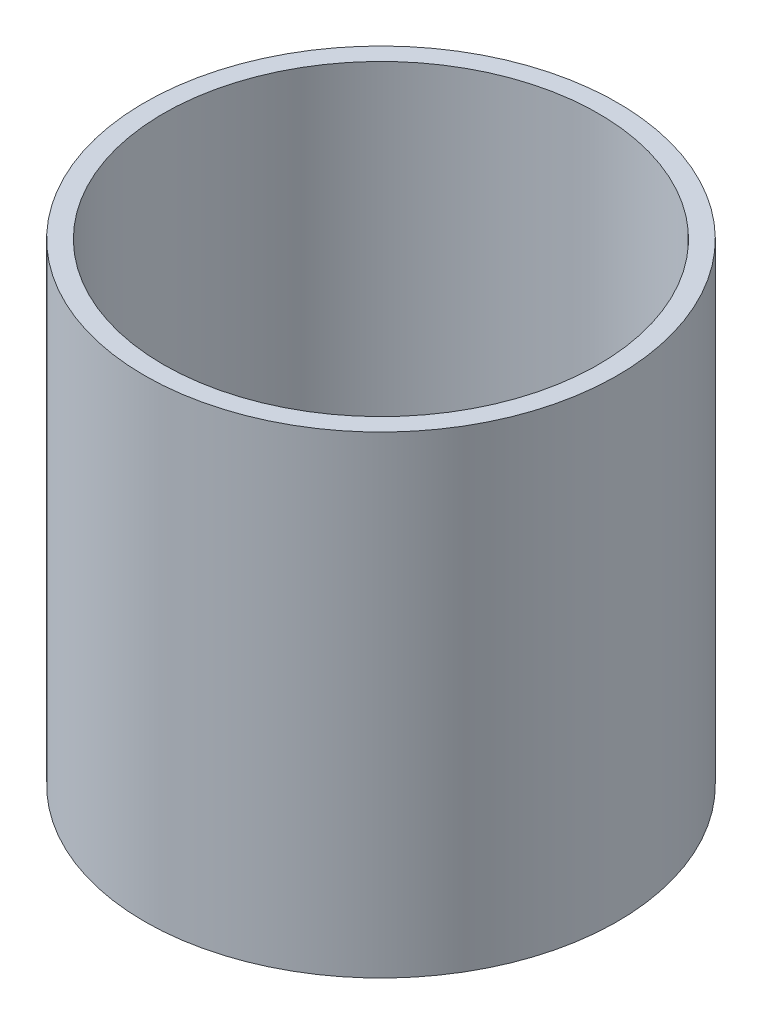
SolidWorks part; units mm, degrees
material "Acrylic (Medium-high impact)"
ref_plane "Front Plane" through (0, 0, 0) normal (0, 0, 1) x (1, 0, 0)
ref_plane "Top Plane" through (0, 0, 0) normal (0, 1, 0) x (1, 0, 0)
ref_plane "Right Plane" through (0, 0, 0) normal (1, 0, 0) x (0, 0, -1)
sketch "Sketch1" plane through (0, 0, 0) normal (0, 1, 0) x (1, 0, 0)
  circle A0 centre (0, 0) radius 3.175
  circle A1 centre (0, 0) radius 2.921
  dimension "D1" = 6.35
  dimension "D2" = 0.254
extrude "Boss-Extrude1" add sketch "Sketch1" along normal blind 6.35
